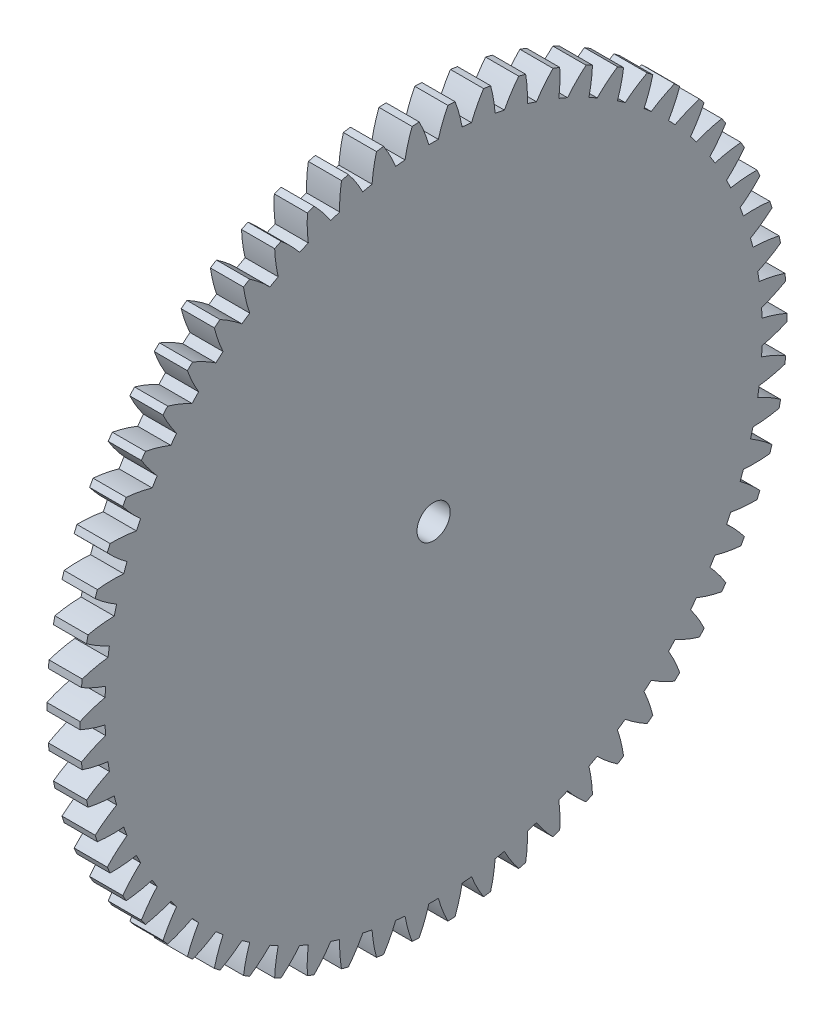
SolidWorks part; units mm, degrees
ref_plane "Plane1" through (0, 0, 0) normal (0, 0, 1) x (1, 0, 0)
ref_plane "Plane2" through (0, 0, 0) normal (0, 1, 0) x (1, 0, 0)
ref_plane "Plane3" through (0, 0, 0) normal (1, 0, 0) x (0, 0, -1)
sketch "HoldingSke" plane through (0, 0, 0) normal (0, 1, 0) x (1, 0, 0)
  line L0 (0, 0) -> (0.4695, -0.8829)
  line L1 (-15, 0) -> (100, 0) construction
  line L2 (0, 0) -> (-2.1039, 2.3779)
  line L3 (0, 0) -> (-11.863, 4.5341)
  line L4 (0, 0) -> (4.0544, 7.6251)
  line L5 (0, 0) -> (-46.8476, -17.4728)
  line L6 (0, 0) -> (-2.4869, -1.6779)
  line L7 (-2.1039, 2.3779) -> (8.6586, 51.2059)
  line L8 (-76.2, 54.61) -> (-75.7, 54.61)
  line L9 (-71.009, 38.7566) -> (-53.1078, 45.2721)
  line L10 (-76.2, 71.12) -> (104.1128, 71.12)
  line L11 (0, 0) -> (-3, 0)
  line L12 (-76.2, 101.6) -> (-76.162, 101.6)
  line L13 (24.9733, 27.94) -> (52.9518, 28.4284)
  line L14 (24.9733, 27.94) -> (24.9743, 27.94)
  line L15 (24.9733, 27.94) -> (100.4006, 29.5858)
  line L16 (-63.627, -1) -> (-12.827, -1)
  circle A0 centre (0, 0) radius 1.5
  circle A1 centre (0, 0) radius 29.749
  circle A2 centre (0, 0) radius 37.5
  circle A3 centre (0, 0) radius 1.5
  dimension "MHD" = 59.498
  dimension "Hub_dia" = 75
  dimension "Bore" = 3
  dimension "MBD" = 3
  dimension "Num_teeth" = 62
  dimension "Pitch" = 1
  dimension "Overall_len" = 50
  dimension "Show_teeth" = 62
  dimension "Thickness" = 3
  dimension "OAL" = 50.0001
  dimension "T_dim" = 0.5
  dimension "Ap" = 20
  dimension "H" = 19.05
  dimension "Pitch_radius" = 180.3128
  dimension "Width" = 3
  dimension "Backlash" = 0.038
  dimension "Addendum_fac" = 1
  dimension "Dedendum_fac" = 1.25
  dimension "Clearance_fac" = 0.25
  dimension "Dedendum_add" = 0.001
  dimension "Module" = 1
sketch "BasProSke" plane through (0, 0, 0) normal (0, 1, 0) x (1, 0, 0)
  line L0 (-10, 0) -> (60, 0) construction
  line L1 (0, 0) -> (0, 32)
  line L2 (0, 0) -> (3, 0)
  line L3 (3, 0) -> (3, 32)
  line L4 (3, 32) -> (0, 32)
  dimension "Thickness" = 3
  dimension "Diameter" = 64
revolve "Base-Revolve" add sketch "BasProSke" angle 360 about L0
sketch "TooCutSke" plane through (0, 0, 0) normal (1, 0, 0) x (0, 0, -1)
  line L1 (0, 0) -> (0, 107) construction
  line L2 (0, 0) -> (-0.8518, 30.9883) construction
  line L3 (0, 0) -> (-3.1394, 61.9038) construction
  line L4 (-0.8518, 30.9883) -> (-1.5697, 30.9519) construction
  arc A0 (0.4289, 29.7459) -> (-0.4289, 29.7459) centre (0, 0) ccw
  arc A1 (1.31, 31.9986) -> (-1.31, 31.9986) centre (0, 0) ccw
  circle A2 centre (0, 0) radius 31 construction
  circle A3 centre (0, 0) radius 29.1305 construction
  arc A4 (-0.4289, 29.7459) -> (-1.31, 31.9986) centre (-12.3625, 26.3771) ccw
  arc A5 (1.31, 31.9986) -> (0.4289, 29.7459) centre (12.3625, 26.3771) ccw
  dimension "Root_dia" = 59.498
  dimension "Overcut_dia" = 64.0508
  dimension "Pitch_dia" = 62
  dimension "Base_dia" = 58.2609
  dimension "Flank_rad" = 12.4
  dimension "Half_ang" = 2.903
  dimension "Half_CT" = 0.7188
extrude "ToothCut" cut sketch "TooCutSke" along normal through all
fillet "Breaks" [suppressed] radius 0.02
fillet "RootFillets" [suppressed] radius 0.251
pattern_circular "TeethCuts" count 62 every 5.806 about axis through (-10, 0, 0) along (1, 0, 0) of "ToothCut", "RootFillets", "Breaks"
sketch "HubNeaOneSke" plane through (0, 0, 0) normal (-1, 0, 0) x (0, 0, 1)
  circle A0 centre (0, 0) radius 29.749
  dimension "Diameter" = 59.498
extrude "HubNearOne" [suppressed] add sketch "HubNeaOneSke" along normal blind 47.0001
sketch "HubNeaBotSke" plane through (0, 0, 0) normal (-1, 0, 0) x (0, 0, 1)
  circle A0 centre (0, 0) radius 29.749
  dimension "Diameter" = 59.498
extrude "HubNearBoth" [suppressed] add sketch "HubNeaBotSke" along normal blind 23.5
ref_plane "FarPln" through (3, 0, 0) normal (1, 0, 0) x (0, 0, -1)
sketch "HubFarSke" plane through (3, 0, 0) normal (1, 0, 0) x (0, 0, -1)
  circle A0 centre (0, 0) radius 29.749
  dimension "Diameter" = 59.498
extrude "HubFar" [suppressed] add sketch "HubFarSke" along normal blind 23.5
sketch "BorSke" plane through (0, 0, 0) normal (1, 0, 0) x (0, 0, -1)
  circle A0 centre (0, 0) radius 1.5
  dimension "Diameter" = 3
extrude "Bore" cut sketch "BorSke" along normal mid plane 100.0001
sketch "KeySke" plane through (0, 0, 0) normal (1, 0, 0) x (0, 0, -1)
  line L0 (-0.6, 0) -> (-0.6, 2)
  line L1 (-0.6, 2) -> (0.6, 2)
  line L2 (0.6, 2) -> (0.6, 0)
  line L3 (0, 0) -> (0, 34) construction
  line L4 (-0.6, 0) -> (0.6, 0)
  dimension "Offset" = 2
  dimension "Width" = 1.2
extrude "Keyway" [suppressed] cut sketch "KeySke" along normal mid plane 100.0001
pattern_circular "Keyway2" [suppressed] count 2 every 90 about axis through (-10, 0, 0) along (1, 0, 0)
equation "' \"Module@HoldingSke\" = 6.35"
equation "' \"Num_teeth@HoldingSke\" = 12"
equation "' \"Ap@HoldingSke\" =  20"
equation "' \"Ap@HoldingSke\" = 20"
equation "' \"Width@HoldingSke\" = 0.5 * 25.4"
equation "' \"Hub_dia@HoldingSke\"= 1 * 25.4"
equation "' \"Hub_dia@HoldingSke\" = 1 * 25.4"
equation "' \"Overall_len@HoldingSke\" = 1.0 * 25.4"
equation "' \"Bore@HoldingSke\" = 0.75 * 25.4"
equation "' \"T_dim@HoldingSke\" = 0.1 * 25.4"
equation "' \"Width@KeySke\" = 0.25 * 25.4"
equation "' \"Show_teeth@HoldingSke\" = 13"
equation "' \"Backlash@HoldingSke\" = 0.009 * 25.4"
equation "' \"Addendum_fac@HoldingSke\" = 1.0"
equation "' \"Dedendum_fac@HoldingSke\" = 1.25"
equation "' \"Dedendum_add@HoldingSke\" = 0.00005 * 25.4"
equation "' \"Clearance_fac@HoldingSke\" = 0.25"
equation "\"Pitch@HoldingSke\" = 1 / \"Module@HoldingSke\""
equation "\"Overcut_dia@TooCutSke\" = (\"Num_teeth@HoldingSke\" + 2 * \"Addendum_fac@HoldingSke\") / \"Pitch@HoldingSke\" + 0.002 * 25.4"
equation "\"Pitch_dia@TooCutSke\" = \"Num_teeth@HoldingSke\" / \"Pitch@HoldingSke\""
equation "\"Base_dia@TooCutSke\" = \"Num_teeth@HoldingSke\" / \"Pitch@HoldingSke\" * cos((\"Ap@HoldingSke\"  * 3.14159265 / 180))"
equation "\"Root_dia@TooCutSke\" = (\"Num_teeth@HoldingSke\" + 2) / \"Pitch@HoldingSke\" - 2 * (\"Addendum_fac@HoldingSke\" + \"Dedendum_fac@HoldingSke\") / \"Pitch@HoldingSke\" - \"Dedendum_add@HoldingSke\" * 2"
equation "\"Half_ang@TooCutSke\" = 180 / \"Num_teeth@HoldingSke\""
equation "\"Half_CT@TooCutSke\" = \"Num_teeth@HoldingSke\" / \"Pitch@HoldingSke\" * sin((3.14159265 / 2 / \"Num_teeth@HoldingSke\")) / 2 - 7 * \"Backlash@HoldingSke\" / 4"
equation "\"Flank_rad@TooCutSke\" = \"Num_teeth@HoldingSke\" / \"Pitch@HoldingSke\" / 5"
equation "\"Radius@RootFillets\" = \"Clearance_fac@HoldingSke\" / \"Pitch@HoldingSke\" + \"Dedendum_add@HoldingSke\""
equation "\"Break_rad@Breaks\" = 0.02 / \"Pitch@HoldingSke\""
equation "\"Thickness@HoldingSke\" = \"Width@HoldingSke\""
equation "\"OAL@HoldingSke\" = \"Thickness@HoldingSke\""
equation "\"MHD@HoldingSke\" = (\"Num_teeth@HoldingSke\" + 2) / \"Pitch@HoldingSke\" - 2 * (\"Addendum_fac@HoldingSke\" + \"Dedendum_fac@HoldingSke\")  / \"Pitch@HoldingSke\" - \"Dedendum_add@HoldingSke\" * 2"
equation "\"MBD@HoldingSke\" = (\"Num_teeth@HoldingSke\" + 2) / \"Pitch@HoldingSke\" - 2 * (\"Addendum_fac@HoldingSke\" + \"Dedendum_fac@HoldingSke\")  / \"Pitch@HoldingSke\" - \"Dedendum_add@HoldingSke\" * 2 - 0.002 * 25.4"
equation "\"MHD@HoldingSke\" = ((sgn( \"MHD@HoldingSke\" - \"Hub_dia@HoldingSke\" )-1)*( \"MHD@HoldingSke\" - \"Hub_dia@HoldingSke\" ))/-2+ \"Hub_dia@HoldingSke\""
equation "\"MBD@HoldingSke\" = ((sgn( \"MBD@HoldingSke\" - \"Bore@HoldingSke\" )-1)*( \"MBD@HoldingSke\" - \"Bore@HoldingSke\" ))/-2+ \"Bore@HoldingSke\""
equation "\"OAL@HoldingSke\" = ((sgn( \"OAL@HoldingSke\" - \"Overall_len@HoldingSke\" )+1)*( \"OAL@HoldingSke\" - \"Overall_len@HoldingSke\" ))/2 + \"Overall_len@HoldingSke\" + 0.000002 * 25.4"
equation "\"Num_teeth@TeethCuts\" = int( \"Show_teeth@HoldingSke\" ) + 1"
equation "\"Num_teeth@TeethCuts\" = ((sgn( \"Num_teeth@TeethCuts\" - \"Num_teeth@HoldingSke\" )-1)*( \"Num_teeth@TeethCuts\" - \"Num_teeth@HoldingSke\" ))/-2+ \"Num_teeth@HoldingSke\""
equation "\"Num_teeth@TeethCuts\" = ((sgn( \"Num_teeth@TeethCuts\" - 2.0)+1)*( \"Num_teeth@TeethCuts\" - 2.0))/2 +2.0"
equation "\"Angle@TeethCuts\" = 360.0 / \"Num_teeth@HoldingSke\""
equation "\"Diameter@BasProSke\" = (\"Num_teeth@HoldingSke\" + 2 * \"Addendum_fac@HoldingSke\") / \"Pitch@HoldingSke\""
equation "\"Thickness@BasProSke\"  = \"Thickness@HoldingSke\""
equation "' \"Fillet_rad@BasProSke\" =  \"Thickness@HoldingSke\" * 0.05"
equation "' \"Fillet_rad@BasProSke\" = \"Thickness@HoldingSke\" * 0.05"
equation "\"MHD@HoldingSke\" = ((sgn( \"MHD@HoldingSke\" - \"Root_dia@TooCutSke\" )-1)*( \"MHD@HoldingSke\" - \"Root_dia@TooCutSke\" ))/-2+ \"Root_dia@TooCutSke\""
equation "\"Diameter@HubNeaOneSke\" = \"MHD@HoldingSke\""
equation "\"Length@HubNearOne\" = \"OAL@HoldingSke\" - \"Thickness@BasProSke\""
equation "\"Diameter@HubNeaBotSke\" = \"MHD@HoldingSke\""
equation "\"Length@HubNearBoth\" = ( \"OAL@HoldingSke\" - \"Thickness@BasProSke\" ) / 2.0"
equation "\"Thickness@FarPln\" = \"Thickness@BasProSke\""
equation "\"Diameter@HubFarSke\" = \"MHD@HoldingSke\""
equation "\"Length@HubFar\" = ( \"OAL@HoldingSke\" - \"Thickness@BasProSke\" ) / 2.0"
equation "\"Diameter@BorSke\" = \"MBD@HoldingSke\""
equation "\"D1@Bore\" = \"OAL@HoldingSke\" * 2.0"
equation "\"D1@Keyway\" = \"OAL@HoldingSke\" * 2.0"
equation "\"Offset@KeySke\" = \"T_dim@HoldingSke\" + \"MBD@HoldingSke\" / 2.0"
